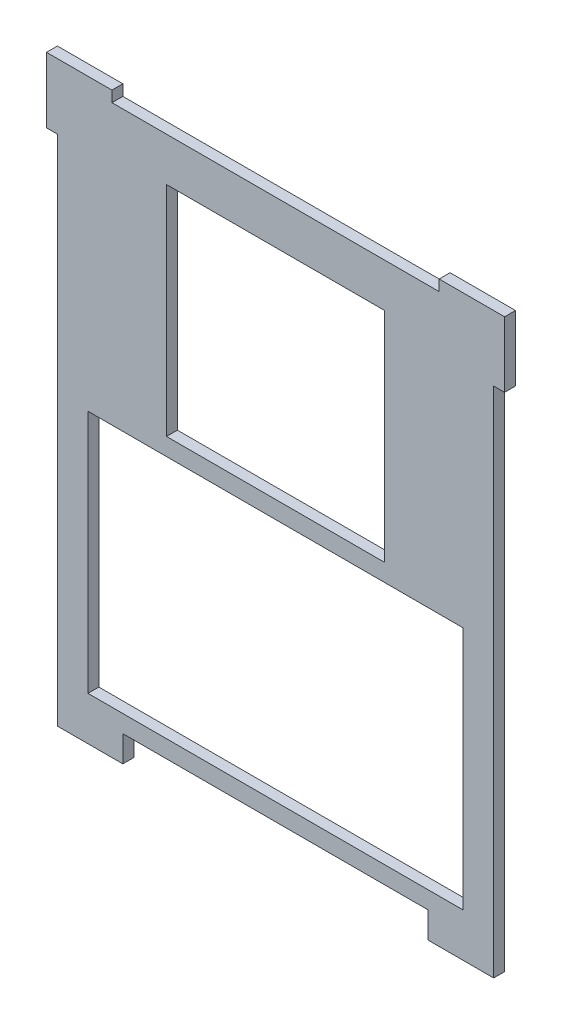
SolidWorks part; units mm, degrees
ref_plane "Front" through (0, 0, 0) normal (0, 0, 1) x (1, 0, 0)
ref_plane "Top" through (0, 0, 0) normal (0, 1, 0) x (1, 0, 0)
ref_plane "Right" through (0, 0, 0) normal (1, 0, 0) x (0, 0, -1)
sketch "Sketch1" plane through (0, 0, 0) normal (0, 0, 1) x (1, 0, 0)
  line L1 (63.5, -88.9) -> (-63.5, -88.9)
  line L2 (63.5, -88.9) -> (63.5, 88.9)
  line L3 (63.5, 88.9) -> (-63.5, 88.9)
  line L4 (-63.5, -88.9) -> (-63.5, 88.9)
  line L5 (63.5, -88.9) -> (-63.5, 88.9) construction
  line L6 (63.5, 88.9) -> (-63.5, -88.9) construction
  point P0 (0, 0)
  dimension "D1" = 177.8
  dimension "D2" = 127
extrude "Boss-Extrude1" add sketch "Sketch1" along normal blind 3.175
sketch "Sketch3" plane through (0, 0, 3.175) normal (0, 0, 1) x (1, 0, 0)
  line L0 (-63.5, 0) -> (63.5, 0) construction
  line L1 (-63.5, 88.9) -> (-63.5, -88.9) construction
  line L2 (63.5, -88.9) -> (63.5, 88.9) construction
  line L3 (0, 0) -> (0, 88.9) construction
  line L4 (63.5, 88.9) -> (-63.5, 88.9) construction
  line L5 (0, -63.5) -> (0, -88.9) construction
  line L6 (-63.5, -88.9) -> (63.5, -88.9) construction
  line L7 (0, 12.7) -> (0, 0) construction
  line L8 (31.75, 12.7) -> (-31.75, 12.7)
  line L9 (31.75, 12.7) -> (31.75, 76.2)
  line L10 (31.75, 76.2) -> (-31.75, 76.2)
  line L11 (-31.75, 12.7) -> (-31.75, 76.2)
  line L12 (31.75, 12.7) -> (-31.75, 76.2) construction
  line L13 (31.75, 76.2) -> (-31.75, 12.7) construction
  line L14 (54.61, -63.5) -> (-54.61, -63.5)
  line L15 (54.61, -63.5) -> (54.61, 7.62)
  line L16 (54.61, 7.62) -> (-54.61, 7.62)
  line L17 (-54.61, -63.5) -> (-54.61, 7.62)
  line L18 (54.61, -63.5) -> (-54.61, 7.62) construction
  line L19 (54.61, 7.62) -> (-54.61, -63.5) construction
  line L20 (0, 76.2) -> (0, 88.9) construction
  point P10 (0, 44.45)
  point P18 (0, -27.94)
  dimension "D1" = 63.5
  dimension "D2" = 63.5
  dimension "D3" = 71.12
  dimension "D4" = 109.22
  dimension "D5" = 25.4
  dimension "D6" = 12.7
  dimension "D7" = 5.08
extrude "Cut-Extrude2" cut sketch "Sketch3" against normal through all
sketch "Sketch4" plane through (0, 0, 3.175) normal (0, 0, 1) x (1, 0, 0)
  line L3 (-60.325, 92.075) -> (-66.675, 92.075)
  line L4 (-66.675, 85.725) -> (-66.675, 92.075)
  line L5 (-60.325, 85.725) -> (-66.675, 92.075) construction
  line L6 (-60.325, 92.075) -> (-66.675, 85.725) construction
  line L9 (60.325, 92.075) -> (66.675, 92.075)
  line L10 (66.675, 85.725) -> (66.675, 92.075)
  line L11 (60.325, 85.725) -> (66.675, 92.075) construction
  line L12 (60.325, 92.075) -> (66.675, 85.725) construction
  line L14 (-66.675, 85.725) -> (-66.675, 73.025)
  line L15 (-66.675, 73.025) -> (-60.325, 73.025)
  line L16 (-60.325, 85.725) -> (-60.325, 73.025)
  line L17 (-60.325, 92.075) -> (-47.625, 92.075)
  line L19 (-60.325, 85.725) -> (-47.625, 85.725)
  line L20 (-47.625, 92.075) -> (-47.625, 85.725)
  line L21 (60.325, 85.725) -> (47.625, 85.725)
  line L23 (60.325, 92.075) -> (47.625, 92.075)
  line L24 (47.625, 85.725) -> (47.625, 92.075)
  line L26 (60.325, 85.725) -> (60.325, 73.025)
  line L27 (60.325, 73.025) -> (66.675, 73.025)
  line L28 (66.675, 85.725) -> (66.675, 73.025)
  point P0 (-63.5, 88.9)
  point P5 (63.5, 88.9)
  dimension "D1" = 6.35
  dimension "D2" = 6.35
  dimension "D3" = 6.35
  dimension "D4" = 6.35
  dimension "D5" = 12.7
  dimension "D6" = 12.7
  dimension "D7" = 12.7
  dimension "D8" = 12.7
extrude "Boss-Extrude2" add sketch "Sketch4" against normal blind 3.175
sketch "Sketch5" plane through (0, 0, 3.175) normal (0, 0, 1) x (1, 0, 0)
  line L1 (-63.5, -88.9) -> (-44.45, -88.9)
  line L2 (-63.5, -88.9) -> (-63.5, -76.2)
  line L3 (-63.5, -76.2) -> (-44.45, -76.2)
  line L4 (-44.45, -88.9) -> (-44.45, -76.2)
  line L5 (63.5, -88.9) -> (44.45, -88.9)
  line L6 (63.5, -88.9) -> (63.5, -76.2)
  line L7 (63.5, -76.2) -> (44.45, -76.2)
  line L8 (44.45, -88.9) -> (44.45, -76.2)
  dimension "D1" = 19.05
  dimension "D2" = 19.05
  dimension "D3" = 12.7
  dimension "D4" = 12.7
extrude "Cut-Extrude3" cut sketch "Sketch5" against normal up to next
sketch "Sketch6" plane through (0, 0, 3.175) normal (0, 0, 1) x (1, 0, 0)
  line L1 (-44.45, -76.2) -> (-44.45, -68.58)
  line L2 (44.45, -76.2) -> (44.45, -68.58)
  line L3 (-44.45, -68.58) -> (44.45, -68.58)
  line L4 (-44.45, -76.2) -> (-44.45, -88.9)
  line L5 (-44.45, -88.9) -> (44.45, -88.9)
  line L6 (44.45, -88.9) -> (44.45, -76.2)
  dimension "D1" = 7.62
extrude "Cut-Extrude4" cut sketch "Sketch6" against normal through all
